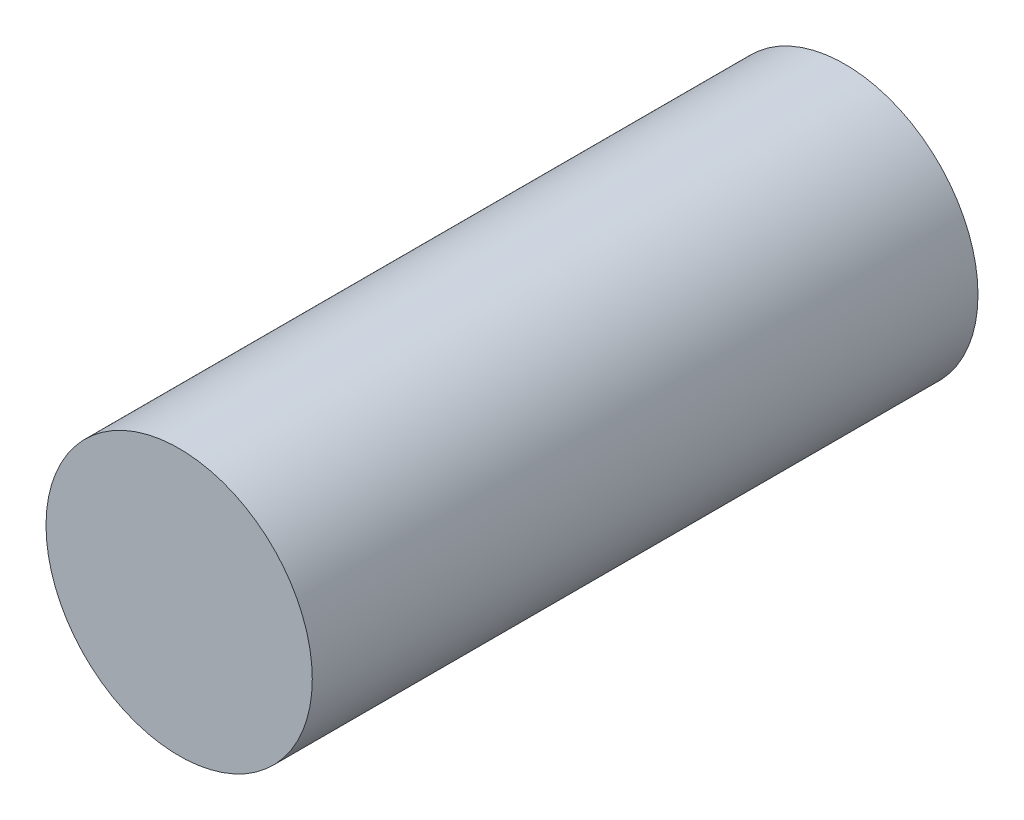
SolidWorks part; units mm, degrees
ref_plane "Plan de face" through (0, 0, 0) normal (0, 0, 1) x (1, 0, 0)
ref_plane "Plan de dessus" through (0, 0, 0) normal (0, 1, 0) x (1, 0, 0)
ref_plane "Plan de droite" through (0, 0, 0) normal (1, 0, 0) x (0, 0, -1)
sketch "Esquisse1" plane through (0, 0, 0) normal (0, 0, 1) x (1, 0, 0)
  circle A0 centre (0, 0) radius 0.2
  dimension "D1" = 0.4
extrude "Boss.-Extru.1" add sketch "Esquisse1" along normal blind 1
